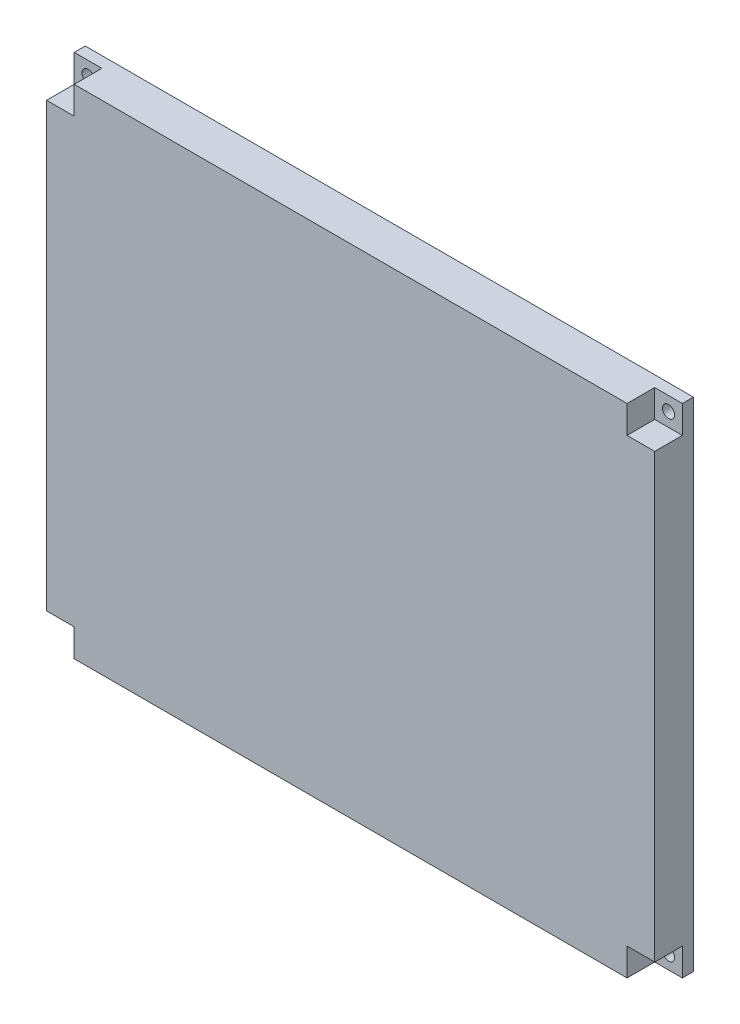
SolidWorks part; units mm, degrees
ref_plane "前基準面" through (0, 0, 0) normal (0, 0, 1) x (1, 0, 0)
ref_plane "上基準面" through (0, 0, 0) normal (0, 1, 0) x (1, 0, 0)
ref_plane "右基準面" through (0, 0, 0) normal (1, 0, 0) x (0, 0, -1)
sketch "草圖1" plane through (0, 0, 0) normal (0, 0, 1) x (1, 0, 0)
  line L1 (-89.0867, 42.9814) -> (30.9133, 42.9814)
  line L2 (-89.0867, 42.9814) -> (-89.0867, -47.0186)
  line L3 (-89.0867, -47.0186) -> (30.9133, -47.0186)
  line L4 (30.9133, 42.9814) -> (30.9133, -47.0186)
  dimension "D1" = 90
  dimension "D2" = 120
extrude "填料-伸長1" add sketch "草圖1" along normal blind 10 contours L4 L3 L2 L1
ref_plane "平面1" through (0, 0, 10) normal (0, 0, 1) x (1, 0, 0)
sketch "草圖6" plane through (0, 0, 10) normal (0, 0, 1) x (1, 0, 0)
  line L0 (-89.0867, -2.0186) -> (30.9133, -2.0186) construction
  line L1 (-89.0867, 42.9814) -> (-89.0867, -47.0186) construction
  line L2 (30.9133, 42.9814) -> (30.9133, -47.0186) construction
  line L3 (-29.0867, 42.9814) -> (-29.0867, -47.0186) construction
  line L4 (-89.0867, 42.9814) -> (30.9133, 42.9814) construction
  line L5 (-89.0867, -47.0186) -> (30.9133, -47.0186) construction
  line L6 (25.9133, 37.9814) -> (20.9133, 37.9814)
  line L7 (-84.0867, 42.9814) -> (-79.0867, 42.9814)
  line L8 (-84.0867, 42.9814) -> (-84.0867, 37.9814)
  line L9 (-84.0867, 37.9814) -> (-79.0867, 37.9814)
  line L10 (-79.0867, 42.9814) -> (-79.0867, 37.9814)
  line L11 (20.9133, 42.9814) -> (20.9133, 37.9814)
  line L12 (25.9133, 42.9814) -> (20.9133, 42.9814)
  line L13 (25.9133, 42.9814) -> (25.9133, 37.9814)
  line L14 (-84.0867, -42.0186) -> (-79.0867, -42.0186)
  line L15 (-79.0867, -47.0186) -> (-79.0867, -42.0186)
  line L16 (-84.0867, -47.0186) -> (-79.0867, -47.0186)
  line L17 (-84.0867, -47.0186) -> (-84.0867, -42.0186)
  line L18 (25.9133, -47.0186) -> (25.9133, -42.0186)
  line L19 (25.9133, -47.0186) -> (20.9133, -47.0186)
  line L20 (20.9133, -47.0186) -> (20.9133, -42.0186)
  line L21 (25.9133, -42.0186) -> (20.9133, -42.0186)
  dimension "D1" = 5
  dimension "D2" = 5
  dimension "D3" = 5
extrude "除料-伸長4" cut sketch "草圖6" against normal blind 5
ref_plane "平面2" through (0, 0, 0) normal (0, 0, -1) x (-1, 0, 0)
sketch "草圖7" plane through (0, 0, 0) normal (0, 0, -1) x (-1, 0, 0)
  line L0 (-30.9133, -2.0186) -> (89.0867, -2.0186) construction
  line L1 (-30.9133, 42.9814) -> (-30.9133, -47.0186) construction
  line L2 (89.0867, 42.9814) -> (89.0867, -47.0186) construction
  line L3 (29.0867, 42.9814) -> (29.0867, -47.0186) construction
  line L4 (89.0867, 42.9814) -> (-30.9133, 42.9814) construction
  line L5 (89.0867, -47.0186) -> (-30.9133, -47.0186) construction
  line L6 (84.0867, 37.9814) -> (79.0867, 37.9814)
  line L7 (-25.9133, 42.9814) -> (-20.9133, 42.9814)
  line L8 (-25.9133, 42.9814) -> (-25.9133, 37.9814)
  line L9 (-25.9133, 37.9814) -> (-20.9133, 37.9814)
  line L10 (-20.9133, 42.9814) -> (-20.9133, 37.9814)
  line L11 (79.0867, 42.9814) -> (79.0867, 37.9814)
  line L12 (84.0867, 42.9814) -> (79.0867, 42.9814)
  line L13 (84.0867, 42.9814) -> (84.0867, 37.9814)
  line L14 (84.0867, -47.0186) -> (84.0867, -42.0186)
  line L15 (84.0867, -47.0186) -> (79.0867, -47.0186)
  line L16 (79.0867, -47.0186) -> (79.0867, -42.0186)
  line L17 (84.0867, -42.0186) -> (79.0867, -42.0186)
  line L18 (-25.9133, -42.0186) -> (-20.9133, -42.0186)
  line L19 (-20.9133, -47.0186) -> (-20.9133, -42.0186)
  line L20 (-25.9133, -47.0186) -> (-20.9133, -47.0186)
  line L21 (-25.9133, -47.0186) -> (-25.9133, -42.0186)
  dimension "D1" = 5
  dimension "D2" = 5
  dimension "D3" = 5
extrude "除料-伸長5" cut sketch "草圖7" against normal blind 3
sketch "草圖8" plane through (0, 0, 0) normal (0, 0, -1) x (-1, 0, 0)
  line L0 (-30.9133, -2.0186) -> (89.0867, -2.0186) construction
  line L1 (-30.9133, 42.9814) -> (-30.9133, -47.0186) construction
  line L2 (89.0867, 42.9814) -> (89.0867, -47.0186) construction
  line L3 (29.0867, 42.9814) -> (29.0867, -47.0186) construction
  line L4 (79.0867, 42.9814) -> (-20.9133, 42.9814) construction
  line L5 (79.0867, -47.0186) -> (-20.9133, -47.0186) construction
  line L6 (-25.9133, 40.4814) -> (-20.9133, 40.4814) construction
  line L7 (-25.9133, 42.9814) -> (-25.9133, 37.9814) construction
  line L8 (-20.9133, 37.9814) -> (-20.9133, 42.9814) construction
  line L9 (-23.4133, 37.9814) -> (-23.4133, 42.9814) construction
  line L10 (-25.9133, 37.9814) -> (-20.9133, 37.9814) construction
  line L11 (-20.9133, 42.9814) -> (-25.9133, 42.9814) construction
  circle A0 centre (-23.4133, 40.4814) radius 1.1
  circle A1 centre (81.5867, 40.4814) radius 1.1
  circle A2 centre (81.5867, -44.5186) radius 1.1
  circle A3 centre (-23.4133, -44.5186) radius 1.1
  dimension "D1" = 2.2
extrude "除料-伸長6" cut sketch "草圖8" against normal blind 42
sketch "草圖10" plane through (0, 0, 0) normal (0, 0, 1) x (1, 0, 0)
  line L1 (-89.0867, 42.9814) -> (30.9133, 42.9814)
  line L2 (-89.0867, 42.9814) -> (-89.0867, -47.0186)
  line L3 (-89.0867, -47.0186) -> (30.9133, -47.0186)
  line L4 (30.9133, 42.9814) -> (30.9133, -47.0186)
extrude "除料-伸長7" cut sketch "草圖10" along normal blind 3
ref_plane "平面3" through (30.9133, 0, 0) normal (1, 0, 0) x (0, 0, -1)
sketch "草圖11" plane through (30.9133, 0, 0) normal (1, 0, 0) x (0, 0, -1)
  line L0 (-10, 49.5) -> (-10, -49.5) construction
  line L1 (-3, 42.9814) -> (-10, 42.9814)
  line L2 (-3, 42.9814) -> (-3, -47.0186)
  line L3 (-3, -47.0186) -> (-10, -47.0186)
  line L4 (-10, 42.9814) -> (-10, -47.0186)
  line L5 (-10, -47.0186) -> (-3, -47.0186) construction
extrude "除料-伸長8" cut sketch "草圖11" against normal blind 5
ref_plane "平面4" through (-89.0867, 0, 0) normal (-1, 0, 0) x (0, 0, 1)
sketch "草圖12" plane through (-89.0867, 0, 0) normal (-1, 0, 0) x (0, 0, 1)
  line L1 (3, 42.9814) -> (10, 42.9814)
  line L2 (3, 42.9814) -> (3, -47.0186)
  line L3 (3, -47.0186) -> (10, -47.0186)
  line L4 (10, 42.9814) -> (10, -47.0186)
extrude "除料-伸長9" cut sketch "草圖12" against normal blind 5
